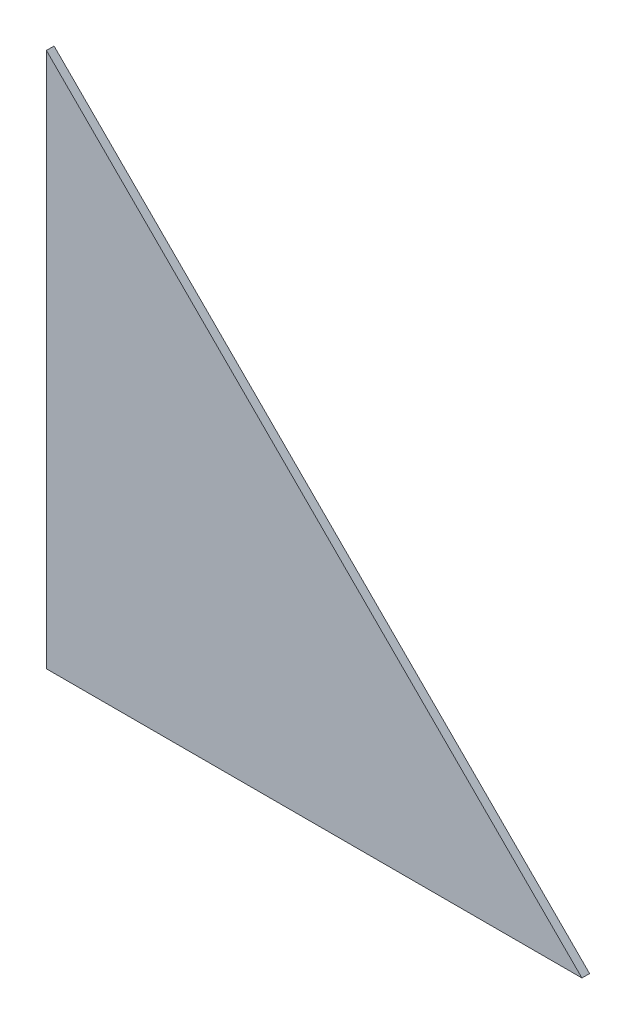
SolidWorks part; units mm, degrees
ref_plane "前视基准面" through (0, 0, 0) normal (0, 0, 1) x (1, 0, 0)
ref_plane "上视基准面" through (0, 0, 0) normal (0, 1, 0) x (1, 0, 0)
ref_plane "右视基准面" through (0, 0, 0) normal (1, 0, 0) x (0, 0, -1)
sketch "草图1" plane through (0, 0, 0) normal (0, 0, 1) x (1, 0, 0)
  line L0 (0, 70) -> (70, 0)
  line L1 (0, 0) -> (70, 0)
  line L2 (0, 0) -> (0, 70)
  dimension "D1" = 70
extrude "凸台-拉伸1" add sketch "草图1" along normal blind 1
